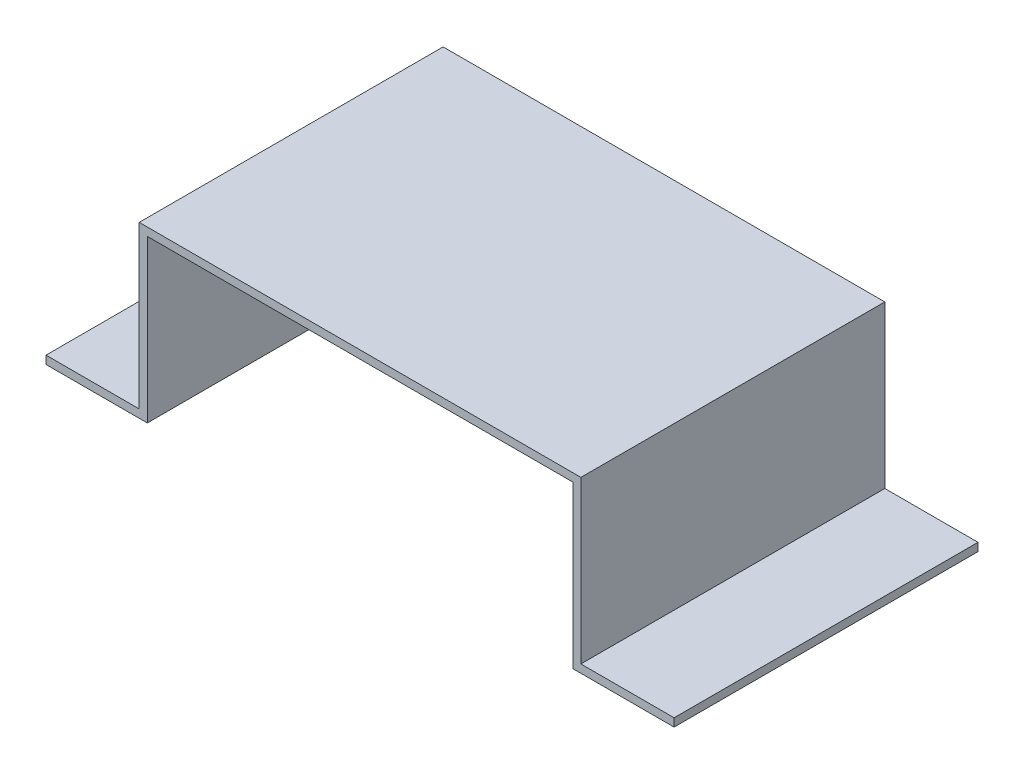
SolidWorks part; units mm, degrees
ref_plane "Front Plane" through (0, 0, 0) normal (0, 0, 1) x (1, 0, 0)
ref_plane "Top Plane" through (0, 0, 0) normal (0, 1, 0) x (1, 0, 0)
ref_plane "Right Plane" through (0, 0, 0) normal (1, 0, 0) x (0, 0, -1)
sketch "Sketch1" plane through (0, 0, 0) normal (0, 0, 1) x (1, 0, 0)
  line L0 (0, 0) -> (25, 0)
  line L1 (25, 0) -> (25, 39.878)
  line L2 (25, 39.878) -> (130, 39.878)
  line L3 (155, 2) -> (155, 0)
  line L4 (77.5, 42.1144) -> (77.5, 0) construction
  line L5 (0, 2) -> (23, 2)
  line L6 (23, 2) -> (23, 41.878)
  line L7 (23, 41.878) -> (132, 41.878)
  line L8 (132, 2) -> (132, 41.878)
  line L9 (23, 41.878) -> (132, 41.878) construction
  line L10 (0, 2) -> (0, 0)
  line L11 (25, 39.878) -> (130, 39.878) construction
  line L12 (130, 0) -> (131.3232, 0) construction
  line L13 (132, 1.882) -> (132, 1.882) construction
  line L14 (130, 39.878) -> (130, 0) construction
  line L15 (132, 41.878) -> (132, 1.882) construction
  line L16 (155, 2) -> (132, 2)
  line L17 (130, 0) -> (130, 39.878)
  line L18 (155, 0) -> (130, 0)
  point P17 (77.5, 39.878)
  point P20 (77.5, 41.878)
  dimension "D2" = 39.878
  dimension "D3" = 25
  dimension "D4" = 105
  dimension "D1" = 2
extrude "Boss-Extrude1" add sketch "Sketch1" along normal blind 75
